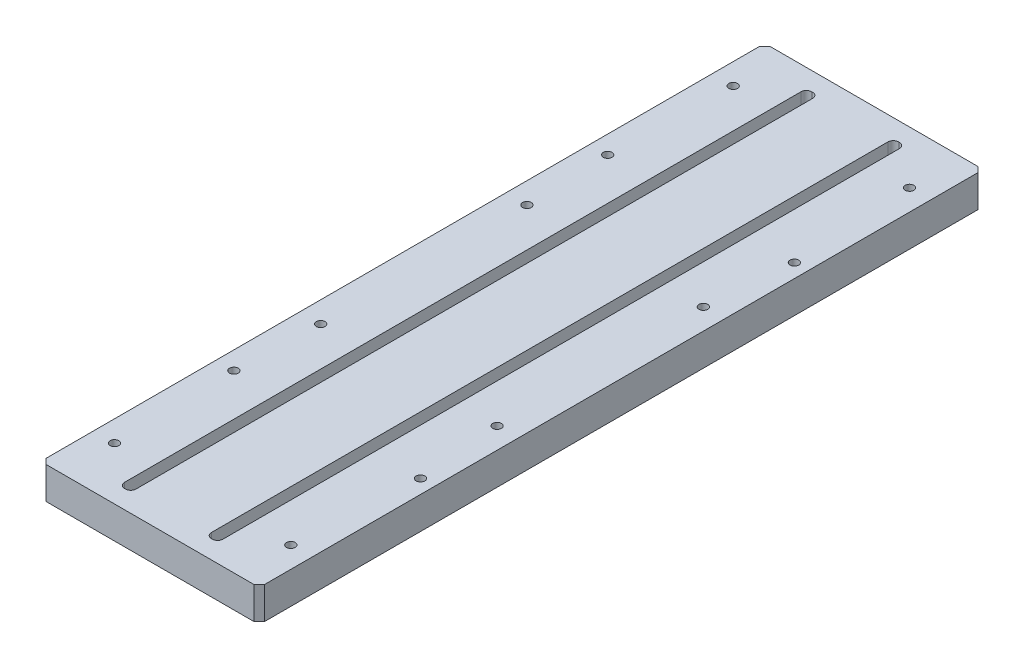
SolidWorks part; units mm, degrees
material "3.3315 (EN-AW 5005)"
ref_plane "Front Plane" through (0, 0, 0) normal (0, 0, 1) x (1, 0, 0)
ref_plane "Top Plane" through (0, 0, 0) normal (0, 1, 0) x (1, 0, 0)
ref_plane "Right Plane" through (0, 0, 0) normal (1, 0, 0) x (0, 0, -1)
sketch "Sketch1" plane through (0, 0, 0) normal (0, 0, 1) x (1, 0, 0)
  line L0 (-10, -2.7) -> (-10, 9.5)
  line L1 (-10, 9.5) -> (10, 9.5)
  line L2 (10, 9.5) -> (10, -2.7)
  line L3 (10, -2.7) -> (8, -2.7)
  line L4 (8, -2.7) -> (8, 2.5)
  line L5 (8, 2.5) -> (4.2, 2.5)
  line L6 (4.2, 2.5) -> (4.2, 0)
  line L7 (4.2, 0) -> (-4.2, 0)
  line L8 (-4.2, 0) -> (-4.2, 2.5)
  line L9 (-4.2, 2.5) -> (-8, 2.5)
  line L10 (-8, 2.5) -> (-8, -2.7)
  line L11 (-8, -2.7) -> (-10, -2.7)
  line L12 (0, 0) -> (0, 9.5) construction
  line L13 (0, -12.5) -> (0, 0) construction
  circle A0 centre (0, -12.5) radius 12.5 construction
  dimension "D4" = 25
  dimension "D1" = 9.5
  dimension "D2" = 3.8
  dimension "D3" = 20
  dimension "D5" = 2
  dimension "D6" = 12.5
  dimension "D7" = 5.2
  dimension "D8" = 2.5
extrude "Boss-Extrude1" add sketch "Sketch1" along normal mid plane 275
sketch "Sketch3" plane through (0, 0, 137.5) normal (0, 0, 1) x (1, 0, 0)
  line L1 (-10, 9.5) -> (10, 9.5)
  line L2 (-10, 9.5) -> (-10, -2.7)
  line L3 (-10, -2.7) -> (10, -2.7)
  line L4 (10, 9.5) -> (10, -2.7)
extrude "Boss-Extrude2" add sketch "Sketch3" against normal blind 2
mirror "Mirror1" about plane through (0, 0, 0) normal (0, 0, 1) of "Boss-Extrude2"
sketch "Sketch2" plane through (0, 9.5, 0) normal (0, 1, 0) x (1, 0, 0)
  line L0 (4.2, -135.5) -> (4.2, 135.5) construction
  line L1 (-2.2, 130.5) -> (2.2, 130.5)
  line L2 (-2.2, 130.5) -> (-2.2, -130.5)
  line L3 (-2.2, -130.5) -> (2.2, -130.5)
  line L4 (2.2, 130.5) -> (2.2, -130.5)
  line L5 (-2.2, 130.5) -> (2.2, -130.5) construction
  line L6 (-2.2, -130.5) -> (2.2, 130.5) construction
  line L8 (4.2, -135.5) -> (8, -135.5) construction
  point P0 (0, 0)
  dimension "D1" = 5
  dimension "D2" = 2
extrude "Cut-Extrude1" cut sketch "Sketch2" against normal through all
fillet "Fillet3" radius 2 4 edges at (-2.2, 4.75, -130.5) (2.2, 4.75, -130.5) (2.2, 4.75, 130.5) (-2.2, 4.75, 130.5)
chamfer "Chamfer1" distance 1 angle 45 8 edges at (2.2, 0, 0) (-2.2, 0, 0) (1.6142, 0, -129.9142) (1.6142, 0, 129.9142) (0, 0, -130.5) (0, 0, 130.5) (-1.6142, 0, -129.9142) (-1.6142, 0, 129.9142)
sketch "Sketch4" plane through (0, 0, 0) normal (0, -1, 0) x (1, 0, 0)
  line L0 (4.2, 135.5) -> (4.2, -135.5) construction
  line L1 (-6.003, 135.5) -> (4.2, 135.5)
  line L2 (-6.003, 135.5) -> (-6.003, 131.5)
  line L3 (-6.003, 131.5) -> (4.2, 131.5)
  line L4 (4.2, 135.5) -> (4.2, 131.5)
  line L5 (-10, 137.5) -> (10, 137.5) construction
  dimension "D1" = 4
  dimension "D2" = 2
extrude "Cut-Extrude2" cut sketch "Sketch4" against normal up to surface (2.5 mm away) up to face at (-6.1, 2.5, 0)
mirror "Mirror2" about plane through (0, 0, 0) normal (0, 0, 1) of "Cut-Extrude2"
chamfer "Chamfer3" [suppressed] distance 1 angle 45
pattern_linear "LPattern2" count 2 spacing 33 along (1, 0, 0) of bodies 106
sketch "Sketch7" plane through (0, 0, -137.5) normal (0, 0, -1) x (-1, 0, 0)
  line L1 (-10, -2.7) -> (-23, -2.7)
  line L2 (-10, -2.7) -> (-10, 9.5)
  line L3 (-10, 9.5) -> (-23, 9.5)
  line L4 (-23, -2.7) -> (-23, 9.5)
extrude "Boss-Extrude3" add sketch "Sketch7" against normal up to vertex
ref_plane "Plane1" through (16.5, 0, 0) normal (-1, 0, 0) x (0, 0, 1)
sketch "Sketch8" plane through (-10, 0, 0) normal (-1, 0, 0) x (0, 0, 1)
  line L4 (-137.5, 9.5) -> (-137.5, -2.7)
  line L5 (-137.5, -2.7) -> (137.5, -2.7)
  line L6 (137.5, -2.7) -> (137.5, 9.5)
  line L7 (137.5, 9.5) -> (-137.5, 9.5)
  line L8 (-137.5, 9.5) -> (-137.5, -2.7)
  line L9 (-137.5, -2.7) -> (137.5, -2.7)
  line L10 (137.5, -2.7) -> (137.5, 9.5)
  line L11 (137.5, 9.5) -> (-137.5, 9.5)
  dimension "D1" = 0
extrude "Boss-Extrude4" add sketch "Sketch8" along normal blind 15
mirror "Mirror4" about plane through (16.5, 0, 0) normal (-1, 0, 0) of "Boss-Extrude4"
hole_wizard "M4 Tapped Hole1" positions "Sketch9" profile "Sketch10" tap size "M4" standard "ISO" end condition through all
sketch "Sketch9" plane through (0, 9.5, 0) normal (0, 1, 0) x (1, 0, 0)
  line L0 (-25, -137.5) -> (-25, 137.5) construction
  line L1 (58, 137.5) -> (-25, 137.5) construction
  point P0 (-17, 117.5)
  dimension "D1" = 8
  dimension "D2" = 20
cosmetic thread "Hole Thread13" parameters "D2"=4
sketch "Sketch10" plane through (-17, 9.5, -117.5) normal (1, 0, 0) x (0, 0, 1)
  line L0 (0, 0) -> (0, 12.2)
  line L1 (0, 12.2) -> (1.65, 12.2)
  line L2 (1.65, 12.2) -> (1.65, 0)
  line L5 (1.65, 0) -> (0, 0)
  line L11 (0, -6.35) -> (0, 107.95) construction
  dimension "Thru Tap Drill Dia." = 3.3
  dimension "Thru Tap Drill Depth" = 12.2
pattern_linear "LPattern3" count 4 spacing 78.3333 along (0, 0, 1) of "M4 Tapped Hole1"
cosmetic thread "Hole Thread14" parameters "D2"=4
cosmetic thread "Hole Thread15" parameters "D2"=4
cosmetic thread "Hole Thread16" parameters "D2"=4
cosmetic thread "Hole Thread17" parameters "D2"=4
mirror "Mirror5" about plane through (16.5, 0, 0) normal (-1, 0, 0) of "LPattern3", "M4 Tapped Hole1"
cosmetic thread "Hole Thread18" parameters "D2"=4
cosmetic thread "Hole Thread19" parameters "D2"=4
cosmetic thread "Hole Thread20" parameters "D2"=4
cosmetic thread "Hole Thread21" parameters "D2"=4
hole_wizard "M4 Tapped Hole2" positions "Sketch11" profile "Sketch12" tap size "M4" standard "ISO" end condition through all
sketch "Sketch11" plane through (0, 9.5, 0) normal (0, 1, 0) x (1, 0, 0)
  point P0 (52.7411, -70.9925)
  point P3 (52.7411, 71.0075)
sketch "Sketch12" plane through (52.7411, 9.5, 70.9925) normal (1, 0, 0) x (0, 0, 1)
  line L0 (0, 0) -> (0, 12.2)
  line L1 (0, 12.2) -> (1.65, 12.2)
  line L2 (1.65, 12.2) -> (1.65, 0)
  line L5 (1.65, 0) -> (0, 0)
  line L11 (0, -6.35) -> (0, 107.95) construction
  dimension "Thru Tap Drill Dia." = 3.3
  dimension "Thru Tap Drill Depth" = 12.2
cosmetic thread "Hole Thread22" parameters "D2"=4
cosmetic thread "Hole Thread23" parameters "D2"=4
fillet "Fillet1" radius 1.5 8 edges at (41, -0.1, 135.5) (25, -0.1, 135.5) (41, -0.1, -135.5) (25, -0.1, -135.5) (-8, -0.1, 135.5) (8, -0.1, 135.5) (-8, -0.1, -135.5) (8, -0.1, -135.5)
chamfer "Chamfer2" distance 0.5 angle 45 16 edges at (33, -2.7, -135.5) (41, -2.7, 0) (25, -2.7, 0) (33, -2.7, 135.5) (0, -2.7, -135.5) (-8, -2.7, 0) (8, -2.7, 0) (0, -2.7, 135.5) (40.5607, -2.7, -135.0607) (25.4393, -2.7, -135.0607) (40.5607, -2.7, 135.0607) (25.4393, -2.7, 135.0607) (-7.5607, -2.7, -135.0607) (7.5607, -2.7, -135.0607) (7.5607, -2.7, 135.0607) (-7.5607, -2.7, 135.0607)
chamfer "Chamfer4" distance 2 angle 45 4 edges at (-25, 3.4, 137.5) (58, 3.4, 137.5) (58, 3.4, -137.5) (-25, 3.4, -137.5)
fillet "Fillet4" radius 1 8 edges at (4.2, 1.25, -131.5) (-4.2, 1.25, 131.5) (-4.2, 1.25, -131.5) (4.2, 1.25, 131.5) (37.2, 1.25, -131.5) (37.2, 1.25, 131.5) (28.8, 1.25, -131.5) (28.8, 1.25, 131.5)
hole_wizard "M4 Tapped Hole3" positions "Sketch13" profile "Sketch14" tap size "M4" standard "ISO" end condition through all
sketch "Sketch13" plane through (0, 9.5, 0) normal (0, 1, 0) x (1, 0, 0)
  point P0 (-18.1589, -70.9925)
  point P3 (-18.1589, 71.0075)
sketch "Sketch14" plane through (-18.1589, 9.5, 70.9925) normal (1, 0, 0) x (0, 0, 1)
  line L0 (0, 0) -> (0, 12.2)
  line L1 (0, 12.2) -> (1.65, 12.2)
  line L2 (1.65, 12.2) -> (1.65, 0)
  line L5 (1.65, 0) -> (0, 0)
  line L11 (0, -6.35) -> (0, 107.95) construction
  dimension "Thru Tap Drill Dia." = 3.3
  dimension "Thru Tap Drill Depth" = 12.2
cosmetic thread "Hole Thread24" parameters "D2"=4
cosmetic thread "Hole Thread25" parameters "D2"=4
